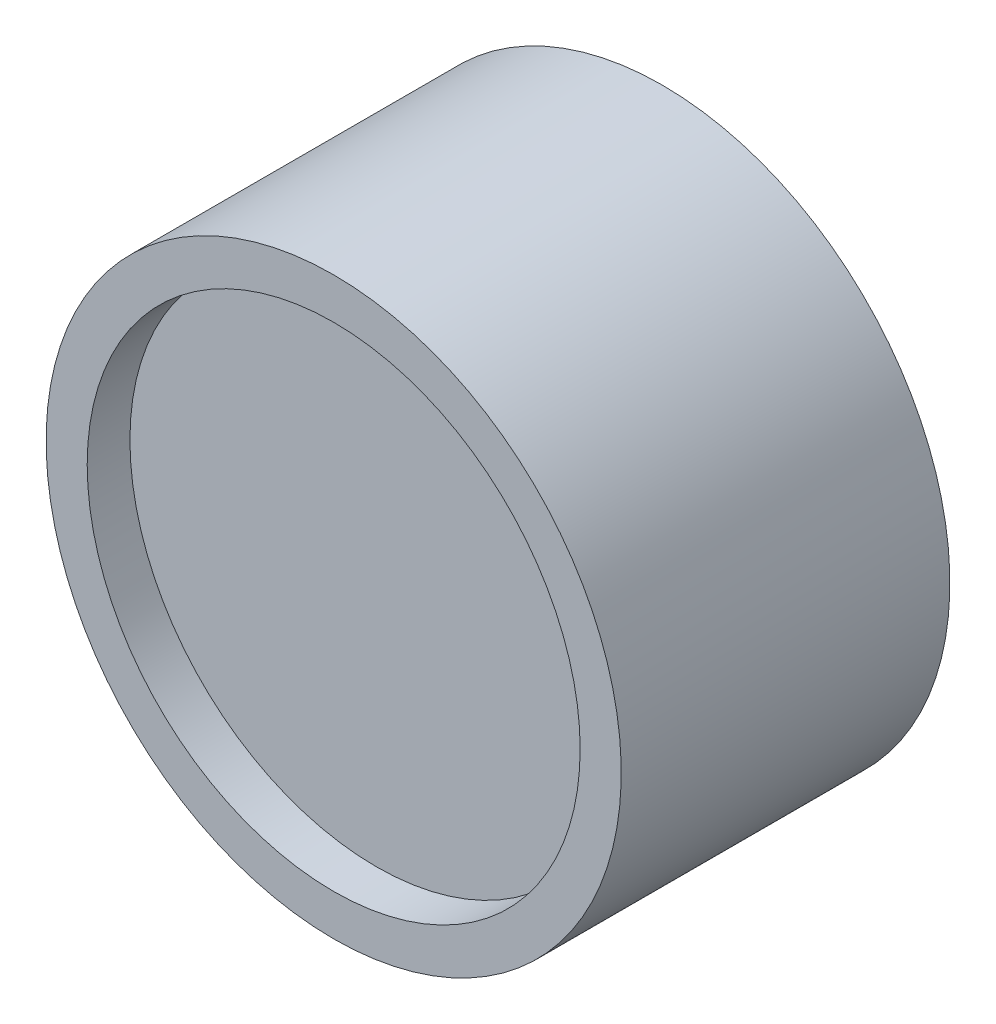
SolidWorks part; units mm, degrees
material "Cast Alloy Steel"
ref_plane "Front" through (0, 0, 0) normal (0, 0, 1) x (1, 0, 0)
ref_plane "Top" through (0, 0, 0) normal (0, 1, 0) x (1, 0, 0)
ref_plane "Right" through (0, 0, 0) normal (1, 0, 0) x (0, 0, -1)
sketch "Sketch1" plane through (0, 0, 0) normal (1, 0, 0) x (0, 0, -1)
  line L0 (0, 0) -> (-9.398, 0)
  line L1 (-9.398, 0) -> (-9.398, 19.05)
  line L2 (-9.398, 19.05) -> (-12.7, 19.05)
  line L3 (-12.7, 19.05) -> (-12.7, 22.225)
  line L4 (-12.7, 22.225) -> (12.7, 22.225)
  line L5 (12.7, 22.225) -> (12.7, 19.05)
  line L6 (12.7, 19.05) -> (9.398, 19.05)
  line L7 (9.398, 19.05) -> (9.398, 0)
  line L8 (9.398, 0) -> (0, 0)
  dimension "D1" = 3.302
  dimension "D2" = 19.05
  dimension "D3" = 22.225
  dimension "D4" = 25.4
revolve "Revolve1" add sketch "Sketch1" angle 360 about L0
ref_plane "Plane1" through (0, -22.225, 0) normal (0, -1, 0) x (-1, 0, 0)
hole_wizard "1/8 (0.125) Diameter Hole1" positions "Sketch2" profile "Sketch3" hole size "1/8" standard "ANSI Inch"
sketch "Sketch2" plane through (0, -22.225, 0) normal (0, -1, 0) x (-1, 0, 0)
  line L2 (-22.225, -12.7) -> (22.225, -12.7) construction
  line L3 (-22.225, 12.7) -> (-22.225, -12.7) construction
  point P0 (0, 0)
  dimension "D1" = 12.7
  dimension "D2" = 22.225
sketch "Sketch3" plane through (0, -22.225, 0) normal (1, 0, 0) x (0, 0, -1)
  line L0 (0, 0) -> (0, 16.8289)
  line L1 (0, 16.8289) -> (1.5875, 15.875)
  line L2 (1.5875, 15.875) -> (1.5875, 0)
  line L5 (1.5875, 0) -> (0, 0)
  line L10 (0, 16.8289) -> (-1.5875, 15.875) construction
  line L11 (0, -6.35) -> (0, 107.95) construction
  dimension "Hole Dia." = 3.175
  dimension "Hole Depth" = 15.875
  dimension "Drill Angle" = 118
